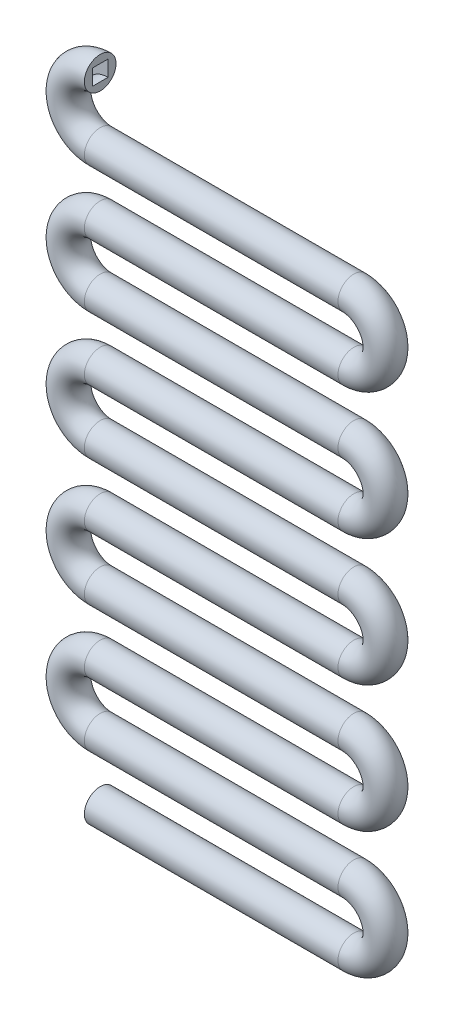
SolidWorks part; units mm, degrees
ref_plane "Plano frontal" through (0, 0, 0) normal (0, 0, 1) x (1, 0, 0)
ref_plane "Plano superior" through (0, 0, 0) normal (0, 1, 0) x (1, 0, 0)
ref_plane "Plano direito" through (0, 0, 0) normal (1, 0, 0) x (0, 0, -1)
sketch "Esboço10" plane through (0, 0, 0) normal (0, 0, 1) x (1, 0, 0)
  line L0 (-80, 0) -> (0, 0)
  line L1 (0, 60) -> (-80, 60)
  line L2 (0, 20) -> (-80, 20)
  line L3 (-80, 40) -> (0, 40)
  line L4 (0, 100) -> (-80, 100)
  line L5 (-80, 80) -> (0, 80)
  line L6 (0, 140) -> (-80, 140)
  line L7 (-80, 120) -> (0, 120)
  line L8 (0, 180) -> (-80, 180)
  line L9 (-80, 160) -> (0, 160)
  arc A0 (0, 20) -> (0, 0) centre (0, 10) cw
  arc A1 (-80, 20) -> (-80, 40) centre (-80, 30) cw
  arc A2 (-80, 60) -> (-80, 80) centre (-80, 70) cw
  arc A3 (0, 60) -> (0, 40) centre (0, 50) cw
  arc A4 (-80, 100) -> (-80, 120) centre (-80, 110) cw
  arc A5 (0, 100) -> (0, 80) centre (0, 90) cw
  arc A6 (-80, 140) -> (-80, 160) centre (-80, 150) cw
  arc A7 (0, 140) -> (0, 120) centre (0, 130) cw
  arc A8 (-80, 180) -> (-80, 200) centre (-80, 190) cw
  arc A9 (0, 180) -> (0, 160) centre (0, 170) cw
  dimension "D2" = 5
  dimension "D4" = 10
  dimension "D1" = 80
ref_plane "Plano1" through (-80, 0, 0) normal (1, 0, 0) x (0, 0, -1)
sketch "Esboço65" plane through (-80, 0, 0) normal (1, 0, 0) x (0, 0, -1)
  line L1 (-2.5, -2.5) -> (2.5, -2.5)
  line L2 (-2.5, -2.5) -> (-2.5, 2.5)
  line L3 (-2.5, 2.5) -> (2.5, 2.5)
  line L4 (2.5, -2.5) -> (2.5, 2.5)
  line L5 (-2.5, -2.5) -> (2.5, 2.5) construction
  line L6 (-2.5, 2.5) -> (2.5, -2.5) construction
  circle A0 centre (0, 0) radius 5
  dimension "D1" = 10
  dimension "D2" = 5
  dimension "D3" = 5
sweep "Varredura5" add profiles "Esboço65" path "Esboço10"
